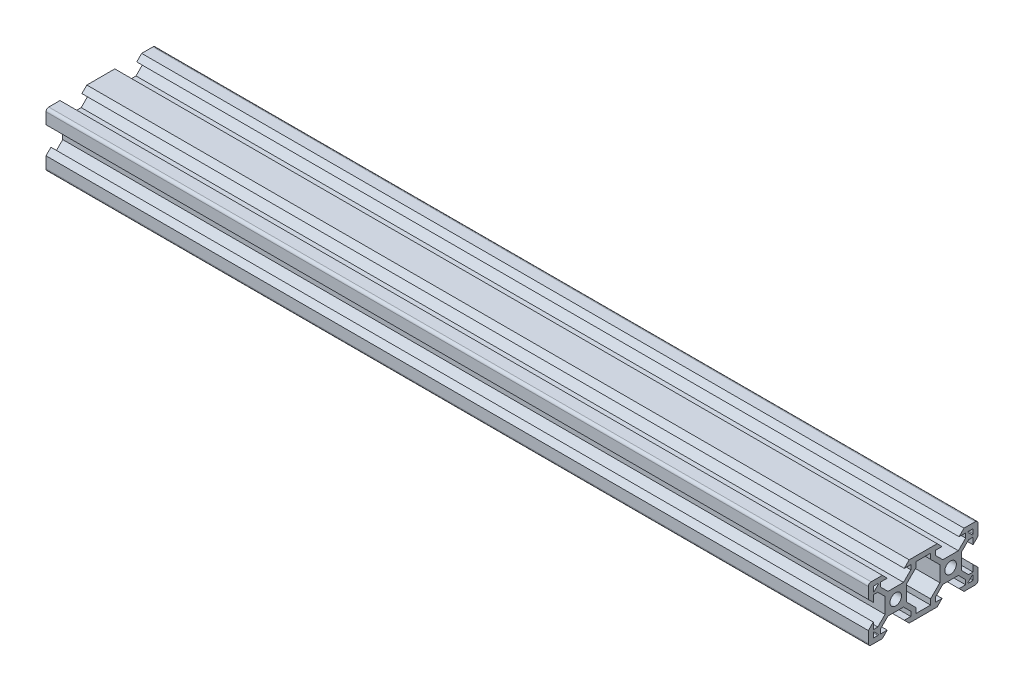
SolidWorks part; units mm, degrees
material "1060 Alloy"
ref_plane "Front Plane" through (0, 0, 0) normal (0, 0, 1) x (1, 0, 0)
ref_plane "Top Plane" through (0, 0, 0) normal (0, 1, 0) x (1, 0, 0)
ref_plane "Right Plane" through (0, 0, 0) normal (1, 0, 0) x (0, 0, -1)
sketch "Sketch4" plane through (0, 0, 0) normal (1, 0, 0) x (0, 0, -1)
  line L0 (-19.2399, 7.0114) -> (20.7601, 7.0114) construction
  dimension "D1" = 40
sketch "Sketch5" plane through (0, 0, 0) normal (1, 0, 0) x (0, 0, -1)
  line L0 (-19.998, 4.9) -> (-18.198, 3.1)
  line L1 (-18.198, 3.1) -> (-18.198, 5.4993)
  line L2 (-18.198, 5.4993) -> (-16.558, 5.4993)
  line L3 (-16.558, 5.4993) -> (-13.9, 2.8413)
  line L4 (-13.9, 2.8413) -> (-13.9, -2.8387)
  line L5 (-13.9, -2.8387) -> (-16.558, -5.4967)
  line L6 (-16.558, -5.4967) -> (-18.198, -5.4967)
  line L7 (-18.198, -5.4967) -> (-18.198, -3.1)
  line L8 (-18.198, -3.1) -> (-19.998, -4.9)
  line L9 (-19.998, -4.9) -> (-19.998, -9)
  line L10 (-18.998, -10) -> (-14.9, -10)
  line L11 (-14.9, -10) -> (-13.1, -8.2)
  line L12 (-13.1, -8.2) -> (-15.5, -8.2)
  line L13 (-15.5, -8.2) -> (-15.5, -6.56)
  line L14 (-15.5, -6.56) -> (-12.84, -3.9)
  line L15 (-12.84, -3.9) -> (-7.16, -3.9)
  line L16 (-7.16, -3.9) -> (-4.5, -6.56)
  line L17 (-4.5, -6.56) -> (-4.5, -8.2)
  line L18 (-4.5, -8.2) -> (-6.9, -8.2)
  line L19 (-6.9, -8.2) -> (-5.1, -10)
  line L20 (-5.1, -10) -> (5.1, -10)
  line L21 (5.1, -10) -> (6.9, -8.2)
  line L22 (6.9, -8.2) -> (4.496, -8.2)
  line L23 (4.496, -8.2) -> (4.496, -6.56)
  line L24 (4.496, -6.56) -> (7.156, -3.9)
  line L25 (7.156, -3.9) -> (12.836, -3.9)
  line L26 (12.836, -3.9) -> (15.496, -6.56)
  line L27 (15.496, -6.56) -> (15.496, -8.2)
  line L28 (15.496, -8.2) -> (13.1, -8.2)
  line L29 (13.1, -8.2) -> (14.9, -10)
  line L30 (14.9, -10) -> (19.002, -10)
  line L31 (20.002, -9) -> (20.002, -4.9)
  line L32 (20.002, -4.9) -> (18.202, -3.1)
  line L33 (18.202, -3.1) -> (18.202, -5.5046)
  line L34 (18.202, -5.5046) -> (16.562, -5.5046)
  line L35 (16.562, -5.5046) -> (13.9, -2.8426)
  line L36 (13.9, -2.8426) -> (13.9, 2.8374)
  line L37 (13.9, 2.8374) -> (16.562, 5.4993)
  line L38 (16.562, 5.4993) -> (18.202, 5.4993)
  line L39 (18.202, 5.4993) -> (18.202, 3.1)
  line L40 (18.202, 3.1) -> (20.002, 4.9)
  line L41 (20.002, 4.9) -> (20.002, 9)
  line L42 (19.002, 10) -> (14.9, 10)
  line L43 (14.9, 10) -> (13.1, 8.2)
  line L44 (13.1, 8.2) -> (15.5013, 8.2)
  line L45 (15.5013, 8.2) -> (15.5013, 6.56)
  line L46 (15.5013, 6.56) -> (12.8413, 3.9)
  line L47 (12.8413, 3.9) -> (7.1613, 3.9)
  line L48 (7.1613, 3.9) -> (4.5013, 6.56)
  line L49 (4.5013, 6.56) -> (4.5013, 8.2)
  line L50 (4.5013, 8.2) -> (6.9, 8.2)
  line L51 (6.9, 8.2) -> (5.1, 10)
  line L52 (5.1, 10) -> (-5.1, 10)
  line L53 (-5.1, 10) -> (-6.9, 8.2)
  line L54 (-6.9, 8.2) -> (-4.5013, 8.2)
  line L55 (-4.5013, 8.2) -> (-4.5013, 6.56)
  line L56 (-4.5013, 6.56) -> (-7.1613, 3.9)
  line L57 (-7.1613, 3.9) -> (-12.8413, 3.9)
  line L58 (-12.8413, 3.9) -> (-15.5013, 6.56)
  line L59 (-15.5013, 6.56) -> (-15.5013, 8.2)
  line L60 (-15.5013, 8.2) -> (-13.1, 8.2)
  line L61 (-13.1, 8.2) -> (-14.9, 10)
  line L62 (-14.9, 10) -> (-18.998, 10)
  line L63 (-19.998, 9) -> (-19.998, 4.9)
  line L64 (6.1, -2.84) -> (6.1, 2.84)
  line L65 (6.1, 2.84) -> (2.7, 6.24)
  line L66 (2.7, 6.24) -> (2.7, 8.2)
  line L67 (2.7, 8.2) -> (-2.7, 8.2)
  line L68 (-2.7, 8.2) -> (-2.7, 6.24)
  line L69 (-2.7, 6.24) -> (-6.1, 2.84)
  line L70 (-6.1, 2.84) -> (-6.1, -2.84)
  line L71 (-6.1, -2.84) -> (-2.7, -6.24)
  line L72 (-2.7, -6.24) -> (-2.7, -8.2)
  line L73 (-2.7, -8.2) -> (2.7, -8.2)
  line L74 (2.7, -8.2) -> (2.7, -6.24)
  line L75 (2.7, -6.24) -> (6.1, -2.84)
  line L76 (0, -8.2) -> (0, 8.2) construction
  line L77 (6.1, 0) -> (-6.1, 0) construction
  line L78 (16.562, 5.4993) -> (15.5013, 6.56) construction
  line L79 (16.5713, 8.2) -> (18.002, 8.2)
  line L81 (17.8606, 6.4279) -> (16.4299, 7.8586)
  line L82 (18.202, 8) -> (18.202, 6.5693)
  line L83 (18.002, 6.5693) -> (18.002, 8) construction
  line L84 (18.002, 8) -> (16.5713, 8) construction
  line L85 (16.5713, 8) -> (18.002, 6.5693) construction
  line L86 (16.5713, -8.2) -> (18.002, -8.2)
  line L87 (18.202, -8) -> (18.202, -6.5693)
  line L88 (17.8606, -6.4279) -> (16.4299, -7.8586)
  line L89 (-17.8606, 6.4279) -> (-16.4299, 7.8586)
  line L90 (-16.5713, 8.2) -> (-18.002, 8.2)
  line L91 (-18.202, 8) -> (-18.202, 6.5693)
  line L92 (-16.5713, -8.2) -> (-18.002, -8.2)
  line L93 (-17.8606, -6.4279) -> (-16.4299, -7.8586)
  line L94 (-18.202, -8) -> (-18.202, -6.5693)
  circle A0 centre (-10, 0) radius 2.1
  circle A1 centre (10, 0) radius 2.1
  arc A2 (-19.998, -9) -> (-18.998, -10) centre (-18.998, -9) ccw
  arc A5 (-18.998, 10) -> (-19.998, 9) centre (-18.998, 9) ccw
  arc A6 (20.002, -9) -> (19.002, -10) centre (19.002, -9) cw
  arc A7 (20.002, 9) -> (19.002, 10) centre (19.002, 9) ccw
  arc A8 (18.002, 8.2) -> (18.202, 8) centre (18.002, 8) cw
  arc A10 (16.4299, 7.8586) -> (16.5713, 8.2) centre (16.5713, 8) cw
  arc A12 (18.202, 6.5693) -> (17.8606, 6.4279) centre (18.002, 6.5693) cw
  arc A13 (16.4299, -7.8586) -> (16.5713, -8.2) centre (16.5713, -8) ccw
  arc A14 (18.002, -8.2) -> (18.202, -8) centre (18.002, -8) ccw
  arc A15 (18.202, -6.5693) -> (17.8606, -6.4279) centre (18.002, -6.5693) ccw
  arc A16 (-18.202, 6.5693) -> (-17.8606, 6.4279) centre (-18.002, 6.5693) ccw
  arc A17 (-16.4299, 7.8586) -> (-16.5713, 8.2) centre (-16.5713, 8) ccw
  arc A18 (-18.002, 8.2) -> (-18.202, 8) centre (-18.002, 8) ccw
  arc A19 (-18.002, -8.2) -> (-18.202, -8) centre (-18.002, -8) cw
  arc A20 (-16.4299, -7.8586) -> (-16.5713, -8.2) centre (-16.5713, -8) cw
  arc A21 (-18.202, -6.5693) -> (-17.8606, -6.4279) centre (-18.002, -6.5693) cw
  dimension "D1" = 4.2
  dimension "D20" = 3.9
  dimension "D27" = 1
  dimension "D40" = 1
  dimension "D41" = 1
  dimension "D42" = 1
  dimension "D45" = 0.2
  dimension "D47" = 1.07
  dimension "D48" = 1.07
  dimension "D49" = 0.2
  dimension "D2" = 20
  dimension "D3" = 10
  dimension "D4" = 5.68
  dimension "D5" = 5.4
  dimension "D6" = 1.96
  dimension "D7" = 45
  dimension "D8" = 1.8
  dimension "D9" = 1.64
  dimension "D10" = 1.8
  dimension "D11" = 40
  dimension "D12" = 20
  dimension "D13" = 3.9
  dimension "D14" = 1.5
  dimension "D15" = 1.5
  dimension "D16" = 3.9
  dimension "D17" = 3.9
  dimension "D18" = 3.9
  dimension "D19" = 3.9
  dimension "D21" = 1.5
  dimension "D22" = 1.5
  dimension "D23" = 1.64
  dimension "D24" = 45
  dimension "D25" = 1.5
  dimension "D26" = 1.8
  dimension "D28" = 6.2
  dimension "D29" = 6.2
  dimension "D30" = 6.2
  dimension "D31" = 6.2
  dimension "D32" = 6.2
  dimension "D33" = 3.1
  dimension "D34" = 3.1
  dimension "D35" = 3.1
  dimension "D36" = 3.1
  dimension "D37" = 6.2
  dimension "D38" = 3.1
  dimension "D39" = 3.1
  dimension "D43" = 1.64
  dimension "D44" = 135
  dimension "D46" = 45
extrude "Boss-Extrude1" add sketch "Sketch5" along normal mid plane 300
